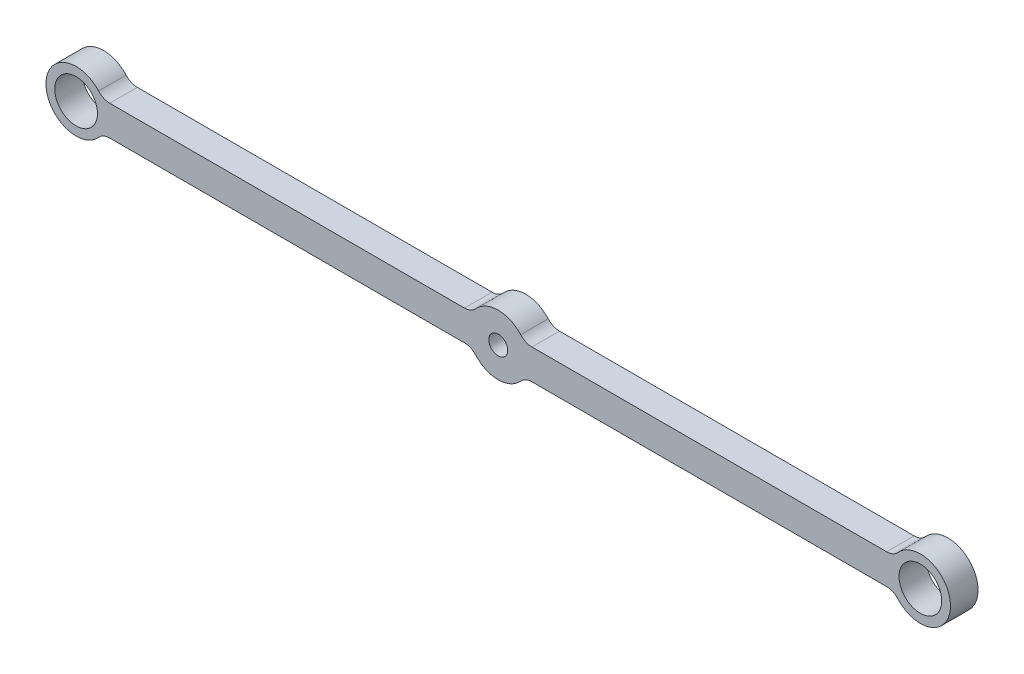
SolidWorks part; units mm, degrees
ref_plane "Front Plane" through (0, 0, 0) normal (0, 0, 1) x (1, 0, 0)
ref_plane "Top Plane" through (0, 0, 0) normal (0, 1, 0) x (1, 0, 0)
ref_plane "Right Plane" through (0, 0, 0) normal (1, 0, 0) x (0, 0, -1)
sketch "Sketch1" plane through (0, 0, 0) normal (0, 0, 1) x (1, 0, 0)
  line L0 (-85.725, 3.175) -> (-85.7116, 3.175)
  line L1 (-88.9, 6.35) -> (88.9, 6.35)
  line L2 (-88.9, 6.35) -> (-88.9, -6.35)
  line L3 (-88.9, -6.35) -> (88.9, -6.35)
  line L4 (88.9, 6.35) -> (88.9, -6.35)
  line L5 (-88.9, 6.35) -> (88.9, -6.35) construction
  line L6 (-88.9, -6.35) -> (88.9, 6.35) construction
  line L8 (-85.725, -3.175) -> (-5.4993, -3.175)
  line L10 (-83.4007, 3.175) -> (-5.4993, 3.175)
  line L11 (-85.725, 3.175) -> (85.725, 3.175) construction
  line L12 (-85.725, 3.175) -> (-85.725, -3.175) construction
  line L13 (-83.4007, -3.175) -> (-5.4993, -3.175)
  line L14 (-85.725, -3.175) -> (85.725, -3.175) construction
  line L15 (5.4993, 3.175) -> (83.4007, 3.175)
  line L16 (5.4993, -3.175) -> (83.4007, -3.175)
  line L17 (85.725, 3.175) -> (85.725, -3.175) construction
  line L18 (85.7116, 3.175) -> (85.725, 3.175)
  line L19 (85.7116, -3.175) -> (85.725, -3.175)
  circle A0 centre (-88.9, 0) radius 6.35
  circle A1 centre (88.9, 0) radius 6.35
  circle A2 centre (-88.9, 0) radius 4.4996
  circle A3 centre (88.9, 0) radius 4.4996
  circle A4 centre (0, 0) radius 1.9939
  circle A5 centre (0, 0) radius 6.35
  point P0 (0, 0)
  point P11 (-88.9, 0)
  point P13 (88.9, 0)
  dimension "D3" = 12.7
  dimension "D4" = 3.175
  dimension "D5" = 8.9992
  dimension "D1" = 3.9878
  dimension "D2" = 177.8
extrude "Boss-Extrude1" add sketch "Sketch1" along normal blind 5.8014 contours A1 L1 A0 L3 | A2 L2 A0 | A2 L2 A0 | A3 L4 A1 | A3 L4 A1 | A2 L2 A0 L8 | A5 L10 A0 L8 | A5 A4
fillet "Fillet1" radius 3.175 8 edges at (-83.4007, -3.175, 2.9007) (5.4993, -3.175, 2.9007) (-5.4993, -3.175, 2.9007) (83.4007, -3.175, 2.9007) (83.4007, 3.175, 2.9007) (-5.4993, 3.175, 2.9007) (5.4993, 3.175, 2.9007) (-83.4007, 3.175, 2.9007)
